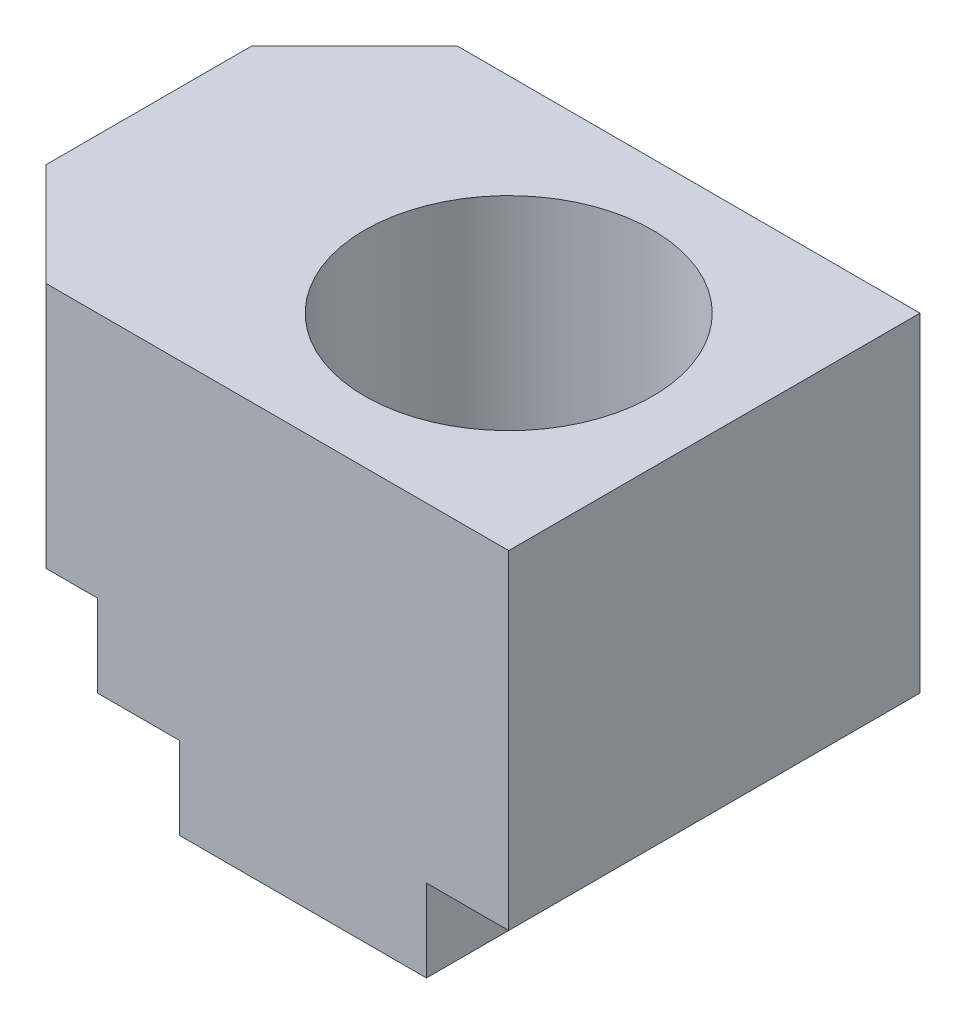
SolidWorks part; units mm, degrees
ref_plane "Plan de face" through (0, 0, 0) normal (0, 0, 1) x (1, 0, 0)
ref_plane "Plan de dessus" through (0, 0, 0) normal (0, 1, 0) x (1, 0, 0)
ref_plane "Plan de droite" through (0, 0, 0) normal (1, 0, 0) x (0, 0, -1)
sketch "Esquisse1" plane through (0, 0, 0) normal (0, 0, 1) x (1, 0, 0)
  line L0 (-49.3756, -19.8819) -> (5.6244, -19.8819)
  line L1 (5.6244, -19.8819) -> (5.6244, 20.1181)
  line L2 (5.6244, 20.1181) -> (-49.3756, 20.1181)
  line L3 (-49.3756, 20.1181) -> (-49.3756, -19.8819)
  dimension "D1" = 55
  dimension "D2" = 40
extrude "Extrusion1" add sketch "Esquisse1" along normal blind 40
sketch "Esquisse2" plane through (0, 0, 40) normal (0, 0, 1) x (1, 0, 0)
  line L0 (5.6244, -19.8819) -> (-2.3756, -19.8819)
  line L1 (-49.3756, -19.8819) -> (5.6244, -19.8819) construction
  line L2 (-2.3756, -19.8819) -> (-2.3756, -11.8819)
  line L3 (-2.3756, -11.8819) -> (5.6244, -11.8819)
  line L4 (5.6244, -19.8819) -> (5.6244, 20.1181) construction
  line L5 (5.6244, -11.8819) -> (5.6244, -19.8819)
  dimension "D1" = 8
  dimension "D2" = 8
extrude "Enlèv. mat.-Extru.1" cut sketch "Esquisse2" against normal through all
sketch "Esquisse3" plane through (0, 0, 40) normal (0, 0, 1) x (1, 0, 0)
  line L0 (-49.3756, -3.8819) -> (-34.3756, -3.8819)
  line L1 (-49.3756, 20.1181) -> (-49.3756, -19.8819) construction
  line L2 (-34.3756, -3.8819) -> (-34.3756, -11.8819)
  line L3 (-34.3756, -11.8819) -> (-26.3756, -11.8819)
  line L4 (-26.3756, -11.8819) -> (-26.3756, -19.8819)
  line L5 (-49.3756, -19.8819) -> (-2.3756, -19.8819) construction
  line L6 (-26.3756, -19.8819) -> (-49.3756, -19.8819)
  line L7 (-49.3756, -19.8819) -> (-49.3756, -3.8819)
  dimension "D1" = 23
  dimension "D2" = 8
  dimension "D3" = 8
  dimension "D4" = 8
extrude "Enlèv. mat.-Extru.2" cut sketch "Esquisse3" against normal blind 40
sketch "Esquisse4" plane through (0, 20.1181, 0) normal (0, 1, 0) x (-1, 0, 0)
  line L0 (49.3756, 0) -> (39.3756, 0)
  line L1 (-5.6244, 0) -> (49.3756, 0) construction
  line L2 (39.3756, 0) -> (49.3756, 10)
  line L3 (49.3756, 40) -> (49.3756, 0) construction
  line L4 (49.3756, 10) -> (49.3756, 0)
  dimension "D1" = 10
  dimension "D2" = 10
extrude "Enlèv. mat.-Extru.3" cut sketch "Esquisse4" against normal blind 40
sketch "Esquisse5" plane through (0, 20.1181, 0) normal (0, 1, 0) x (-1, 0, 0)
  line L0 (49.3756, 30) -> (39.3756, 40)
  line L1 (49.3756, 40) -> (49.3756, 10) construction
  line L2 (-5.6244, 40) -> (49.3756, 40) construction
  line L3 (39.3756, 40) -> (49.3756, 40)
  line L4 (49.3756, 40) -> (49.3756, 30)
  dimension "D1" = 10
  dimension "D2" = 10
extrude "Enlèv. mat.-Extru.4" cut sketch "Esquisse5" against normal blind 40
sketch "Esquisse6" plane through (0, 20.1181, 0) normal (0, 1, 0) x (-1, 0, 0)
  line L0 (-5.6244, 0) -> (39.3756, 0) construction
  line L1 (-5.6244, 40) -> (-5.6244, 0) construction
  circle A0 centre (14.3756, 20) radius 8
  dimension "D1" = 16
  dimension "D2" = 20
  dimension "D3" = 20
extrude "Enlèv. mat.-Extru.5" cut sketch "Esquisse6" against normal through all
sketch "Esquisse7" plane through (0, 20.1181, 0) normal (0, 1, 0) x (-1, 0, 0)
  line L0 (-5.6244, 40) -> (39.3756, 40) construction
  line L1 (-5.6244, 40) -> (-5.6244, 0) construction
  circle A0 centre (14.3756, 20) radius 14
  dimension "D1" = 28
  dimension "D2" = 20
  dimension "D3" = 20
extrude "Enlèv. mat.-Extru.6" cut sketch "Esquisse7" against normal blind 20
